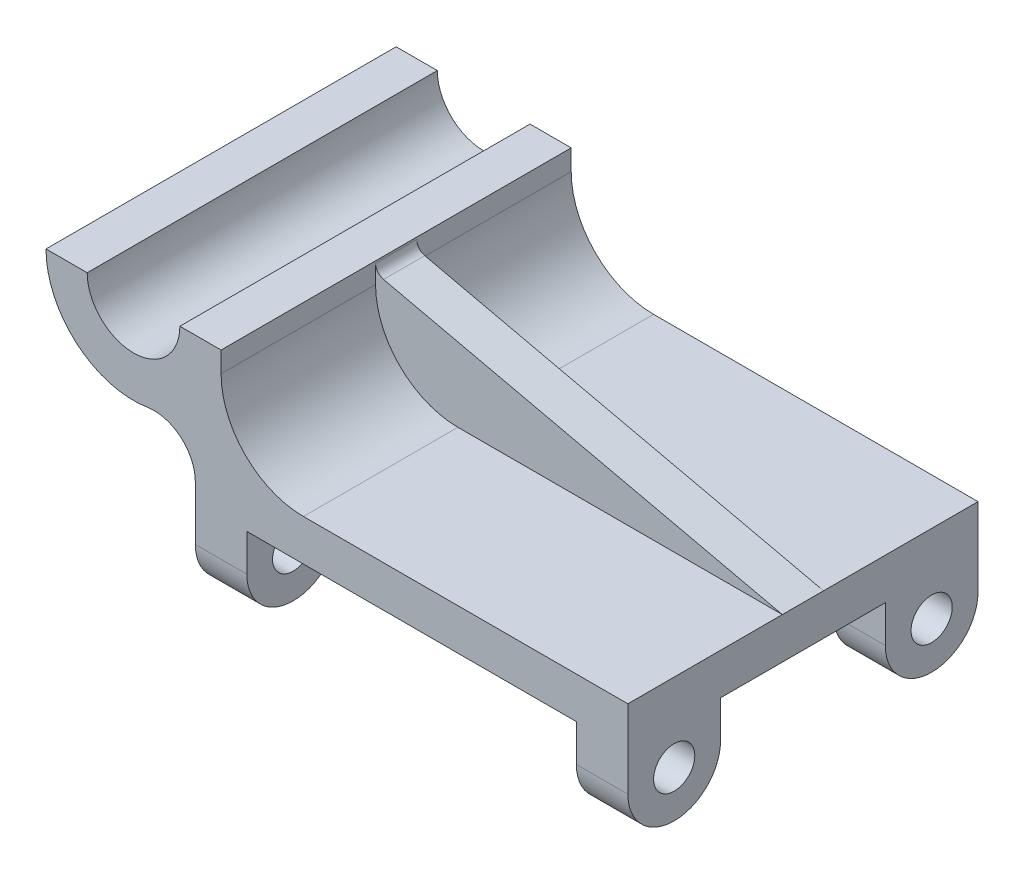
SolidWorks part; units mm, degrees
ref_plane "Front Plane" through (0, 0, 0) normal (0, 0, 1) x (1, 0, 0)
ref_plane "Top Plane" through (0, 0, 0) normal (0, 1, 0) x (1, 0, 0)
ref_plane "Right Plane" through (0, 0, 0) normal (1, 0, 0) x (0, 0, -1)
sketch "Sketch1" plane through (0, 0, 0) normal (0, 0, 1) x (1, 0, 0)
  line L0 (120.65, 0) -> (-12.7, 0)
  line L1 (120.65, 0) -> (120.65, 12.7)
  line L2 (120.65, 12.7) -> (20.6375, 12.7)
  line L3 (-58.7375, 44.45) -> (-46.0375, 44.45)
  line L4 (-17.4625, 44.45) -> (-4.7625, 44.45)
  line L5 (-12.7, 5.2738) -> (-12.7, 0)
  line L6 (-4.7625, 44.45) -> (-4.7625, 38.1)
  arc A0 (-46.0375, 44.45) -> (-17.4625, 44.45) centre (-31.75, 44.45) ccw
  arc A1 (-12.7, 5.2738) -> (-27.432, 17.8102) centre (-25.4, 5.2738) ccw
  arc A2 (-58.7375, 44.45) -> (-27.432, 17.8102) centre (-31.75, 44.45) ccw
  arc A3 (20.6375, 12.7) -> (-4.7625, 38.1) centre (20.6375, 38.1) cw
  dimension "D3" = 25.4
  dimension "D5" = 19.05
  dimension "D7" = 25.4
  dimension "D4" = 28.575
  dimension "D6" = 53.975
  dimension "D1" = 133.35
  dimension "D2" = 12.7
extrude "Boss-Extrude1" add sketch "Sketch1" along normal mid plane 107.95
sketch "Sketch3" plane through (120.65, 0, 0) normal (1, 0, 0) x (0, 0, -1)
  line L1 (-53.975, -11.4313) -> (-53.975, 0)
  line L2 (-25.4, -11.4313) -> (-25.4, 0)
  line L3 (-53.975, 0) -> (53.975, 0) construction
  line L4 (-53.975, 0) -> (-25.4, 0)
  line L5 (0, 12.7) -> (0, 0) construction
  line L6 (-53.975, 12.7) -> (53.975, 12.7) construction
  line L7 (53.975, 0) -> (25.4, 0)
  line L8 (25.4, -11.4313) -> (25.4, 0)
  line L9 (53.975, -11.4313) -> (53.975, 0)
  circle A0 centre (-39.6875, -11.4313) radius 6.35
  arc A1 (-53.975, -11.4313) -> (-25.4, -11.4313) centre (-39.6875, -11.4313) ccw
  arc A2 (53.975, -11.4313) -> (25.4, -11.4313) centre (39.6875, -11.4313) cw
  circle A3 centre (39.6875, -11.4313) radius 6.35
  dimension "D1" = 12.7
  dimension "D3" = 28.575
  dimension "D4" = 11.4313
  dimension "D2" = 14.2875
extrude "Boss-Extrude2" add sketch "Sketch3" against normal up to surface (133.35 mm away) up to face at (-12.7, 2.6369, 0)
sketch "Sketch4" plane through (0, 0, 53.975) normal (0, 0, 1) x (1, 0, 0)
  line L0 (-12.7, -25.7188) -> (120.65, -25.7188) construction
  line L1 (3.175, -25.7188) -> (104.775, -25.7188)
  line L2 (3.175, -25.7188) -> (3.175, 0)
  line L3 (3.175, 0) -> (104.775, 0)
  line L4 (104.775, -25.7188) -> (104.775, 0)
  line L5 (120.65, 12.7) -> (20.6375, 12.7) construction
  line L6 (120.65, -11.4313) -> (120.65, 12.7) construction
  line L7 (-12.7, -11.4313) -> (-12.7, -25.7188) construction
  dimension "D1" = 12.7
  dimension "D2" = 15.875
  dimension "D3" = 15.875
extrude "Cut-Extrude1" cut sketch "Sketch4" against normal through all
sketch "Sketch5" plane through (0, 0, 0) normal (0, 0, 1) x (1, 0, 0)
  line L0 (120.65, 12.7) -> (-6.6817, 41.7123)
  line L2 (-4.7625, 44.45) -> (-17.4625, 44.45) construction
  dimension "D1" = 2.7377
  dimension "D2" = 130.5951
rib "Rib3" sketch "Sketch5" sketch "Sketch5" thickness 12.7 extrusion direction parallel to sketch draft on no parameters "D1"=12.7
fillet "Fillet1" radius 3.175 1 edges at (-4.7625, 41.275, 0)
